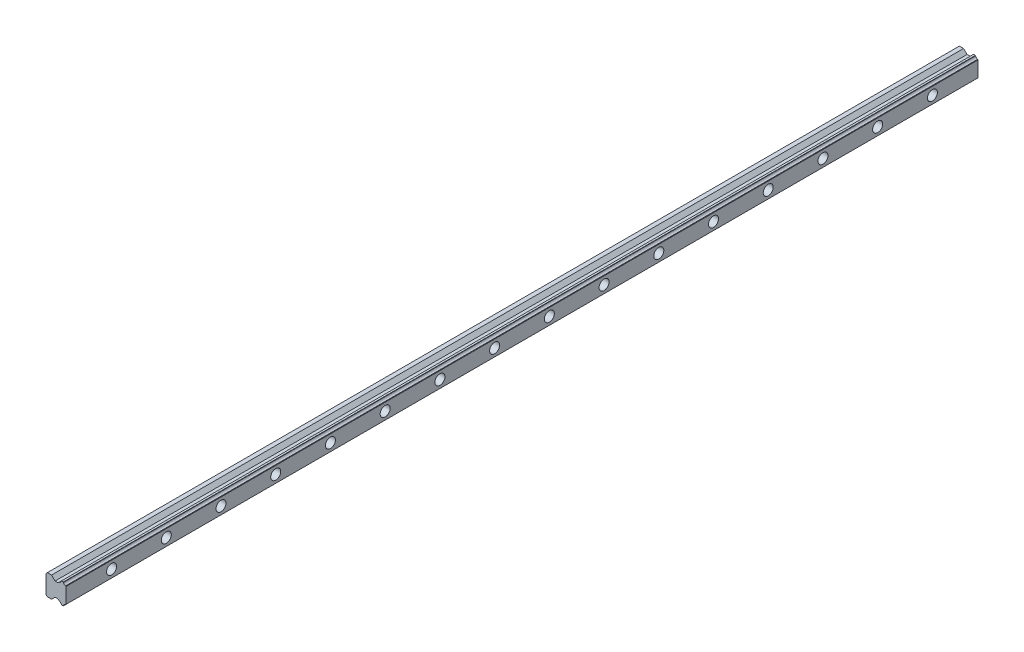
SolidWorks part; units mm, degrees
material "1.4003 (X2CrNi12)"
ref_plane "Plano frontal" through (0, 0, 0) normal (0, 0, 1) x (1, 0, 0)
ref_plane "Plano superior" through (0, 0, 0) normal (0, 1, 0) x (1, 0, 0)
ref_plane "Plano direito" through (0, 0, 0) normal (1, 0, 0) x (0, 0, -1)
sketch "Esboço2" plane through (0, 0, 0) normal (0, 0, 1) x (1, 0, 0)
  line L0 (-1.1493, 21.3931) -> (-1.1493, 1.3931)
  line L1 (-1.1493, 1.3931) -> (0.3507, -0.1069)
  line L2 (0.3507, -0.1069) -> (4.9494, -0.1069)
  line L3 (4.9494, -0.1069) -> (8.7494, 3.6931)
  line L4 (8.7494, 3.6931) -> (12.1309, 3.6931)
  line L5 (12.1309, 3.6931) -> (13.3606, 2.4634)
  line L6 (15.6254, 0.1986) -> (15.8309, -0.0069)
  line L7 (15.8309, -0.0069) -> (17.8594, -0.0069)
  line L8 (17.8594, -0.0069) -> (18.0771, 0.2107)
  line L9 (20.3285, 2.4621) -> (20.7507, 2.8844)
  line L10 (20.7507, 2.8844) -> (20.7507, 19.9018)
  line L11 (20.7507, 19.9018) -> (20.3285, 20.324)
  line L12 (18.0771, 22.5754) -> (17.8594, 22.7931)
  line L13 (17.8594, 22.7931) -> (15.8309, 22.7931)
  line L14 (15.8309, 22.7931) -> (15.6254, 22.5876)
  line L15 (13.3606, 20.3228) -> (12.1309, 19.0931)
  line L16 (12.1309, 19.0931) -> (8.7494, 19.0931)
  line L17 (8.7494, 19.0931) -> (4.9494, 22.8931)
  line L18 (4.9494, 22.8931) -> (0.3507, 22.8931)
  line L19 (0.3507, 22.8931) -> (-1.1493, 21.3931)
  arc A0 (13.3606, 20.3228) -> (15.6254, 22.5876) centre (13.108, 22.8401) ccw
  arc A1 (18.0771, 22.5754) -> (20.3285, 20.324) centre (20.5932, 22.8401) ccw
  arc A2 (20.3285, 2.4621) -> (18.0771, 0.2107) centre (20.5932, -0.054) ccw
  arc A3 (13.3606, 2.4634) -> (15.6254, 0.1986) centre (13.108, -0.054) cw
  dimension "D4" = 2.53
  dimension "D5" = 2.53
  dimension "D6" = 2.53
  dimension "D7" = 2.53
  dimension "D1" = 2.0286
  dimension "D2" = 17.0174
  dimension "D3" = 21.9
extrude "Ressalto-extrusão1" add sketch "Esboço2" along normal blind 1000
sketch "Esboço4" plane through (20.7507, 0, 0) normal (1, 0, 0) x (0, 0, -1)
  line L0 (0, 2.8844) -> (0, 19.9018) construction
  circle A0 centre (-50, 11.3931) radius 3.5
  circle A1 centre (-110, 11.3931) radius 3.5
  circle A2 centre (-170, 11.3931) radius 3.5
  circle A3 centre (-230, 11.3931) radius 3.5
  circle A4 centre (-290, 11.3931) radius 3.5
  circle A5 centre (-350, 11.3931) radius 3.5
  circle A6 centre (-410, 11.3931) radius 3.5
  circle A7 centre (-470, 11.3931) radius 3.5
  circle A8 centre (-530, 11.3931) radius 3.5
  circle A9 centre (-590, 11.3931) radius 3.5
  circle A10 centre (-650, 11.3931) radius 3.5
  circle A11 centre (-710, 11.3931) radius 3.5
  circle A12 centre (-770, 11.3931) radius 3.5
  circle A13 centre (-830, 11.3931) radius 3.5
  circle A14 centre (-890, 11.3931) radius 3.5
  circle A15 centre (-950, 11.3931) radius 3.5
  dimension "D1" = 50
  dimension "D2" = 7
  dimension "D3" = 16
extrude "Corte-extrusão1" cut sketch "Esboço4" against normal through all
sketch "Esboço5" plane through (20.7507, 0, 0) normal (1, 0, 0) x (0, 0, -1)
  circle A0 centre (-50, 11.3931) radius 5.5
  circle A1 centre (-110, 11.3931) radius 5.5
  circle A2 centre (-170, 11.3931) radius 5.5
  circle A3 centre (-230, 11.3931) radius 5.5
  circle A4 centre (-290, 11.3931) radius 5.5
  circle A5 centre (-350, 11.3931) radius 5.5
  circle A6 centre (-410, 11.3931) radius 5.5
  circle A7 centre (-470, 11.3931) radius 5.5
  circle A8 centre (-530, 11.3931) radius 5.5
  circle A9 centre (-590, 11.3931) radius 5.5
  circle A10 centre (-650, 11.3931) radius 5.5
  circle A11 centre (-710, 11.3931) radius 5.5
  circle A12 centre (-770, 11.3931) radius 5.5
  circle A13 centre (-830, 11.3931) radius 5.5
  circle A14 centre (-890, 11.3931) radius 5.5
  circle A15 centre (-950, 11.3931) radius 5.5
  dimension "D1" = 16
extrude "Corte-extrusão2" cut sketch "Esboço5" against normal blind 8.9
